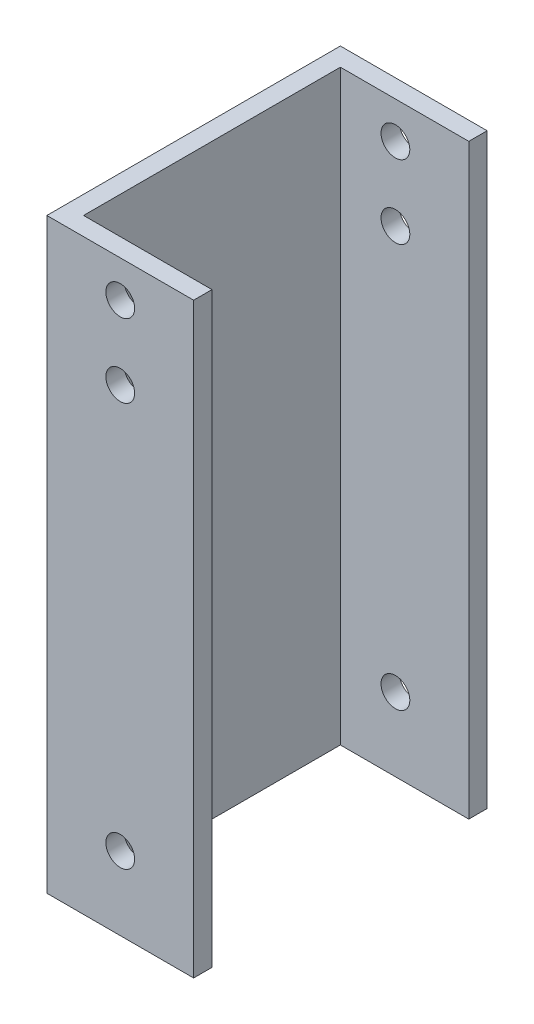
SolidWorks part; units mm, degrees
material "6061-T6 (SS)"
ref_plane "Front Plane" through (0, 0, 0) normal (0, 0, 1) x (1, 0, 0)
ref_plane "Top Plane" through (0, 0, 0) normal (0, 1, 0) x (1, 0, 0)
ref_plane "Right Plane" through (0, 0, 0) normal (1, 0, 0) x (0, 0, -1)
sketch "Sketch1" plane through (0, 0, 0) normal (0, 1, 0) x (1, 0, 0)
  line L0 (0, 0) -> (25.4, 0)
  line L1 (25.4, 0) -> (25.4, 3.175)
  line L2 (25.4, 3.175) -> (3.175, 3.175)
  line L3 (3.175, 3.175) -> (3.175, 47.625)
  line L4 (3.175, 47.625) -> (25.4, 47.625)
  line L5 (25.4, 47.625) -> (25.4, 50.8)
  line L6 (25.4, 50.8) -> (0, 50.8)
  line L7 (0, 50.8) -> (0, 0)
  line L8 (0, 25.4) -> (3.175, 25.4) construction
  dimension "D1" = 50.8
  dimension "D2" = 25.4
  dimension "D3" = 3.175
extrude "Boss-Extrude1" add sketch "Sketch1" along normal blind 101.6
sketch "Sketch2" plane through (0, 0, -50.8) normal (0, 0, -1) x (-1, 0, 0)
  line L0 (-12.7, 101.6) -> (-12.7, 0) construction
  line L1 (-25.4, 101.6) -> (0, 101.6) construction
  line L2 (-25.4, 0) -> (0, 0) construction
  circle A0 centre (-12.7, 12.7) radius 2.4892
  circle A1 centre (-12.7, 95.25) radius 2.4892
  circle A2 centre (-12.7, 82.55) radius 2.4892
  dimension "D1" = 4.9784
  dimension "D2" = 12.7
  dimension "D3" = 6.35
  dimension "D4" = 12.7
extrude "Cut-Extrude1" cut sketch "Sketch2" against normal through all
equation "\"Thick\"= \"in\""
